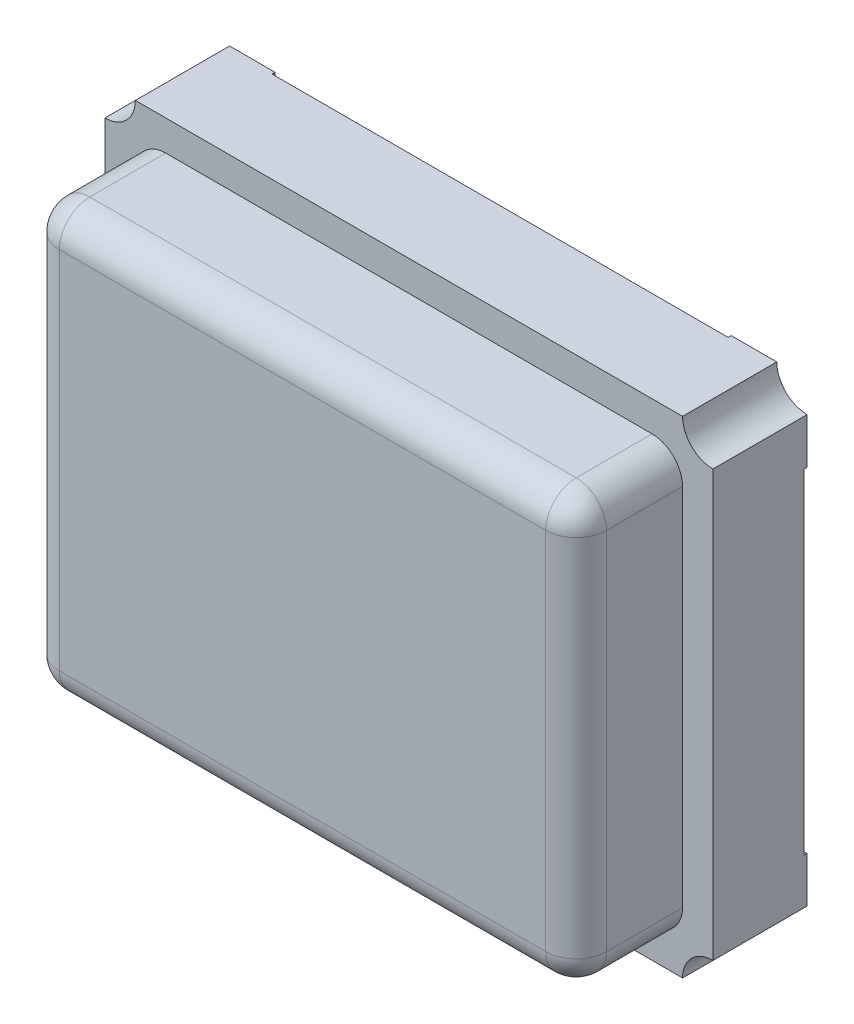
SolidWorks part; units mm, degrees
ref_plane "Front Plane" through (0, 0, 0) normal (0, 0, 1) x (1, 0, 0)
ref_plane "Top Plane" through (0, 0, 0) normal (0, 1, 0) x (1, 0, 0)
ref_plane "Right Plane" through (0, 0, 0) normal (1, 0, 0) x (0, 0, -1)
sketch "Sketch1" plane through (0, 0, 0) normal (0, 0, 1) x (1, 0, 0)
  line L1 (0, 0) -> (2, 0)
  line L2 (0, 0) -> (0, 1.6)
  line L3 (0, 1.6) -> (2, 1.6)
  line L4 (2, 0) -> (2, 1.6)
  dimension "D1" = 2
  dimension "D2" = 1.6
extrude "Boss-Extrude1" add sketch "Sketch1" along normal blind 0.3
sketch "Sketch2" plane through (0, 0, 0.3) normal (0, 0, 1) x (1, 0, 0)
  line L0 (1, 1.6) -> (1, 0) construction
  line L1 (0.1, 0.1) -> (1.9, 0.1)
  line L2 (0.1, 0.1) -> (0.1, 1.5)
  line L3 (0.1, 1.5) -> (1.9, 1.5)
  line L4 (1.9, 0.1) -> (1.9, 1.5)
  line L5 (2, 1.6) -> (0, 1.6) construction
  line L6 (0, 0) -> (2, 0) construction
  line L8 (0, 1.6) -> (0, 0) construction
  line L9 (0, 0.8) -> (2, 0.8) construction
  line L10 (2, 0) -> (2, 1.6) construction
  point P10 (1, 1.5)
  point P17 (0.1, 0.8)
  dimension "D1" = 1.8
  dimension "D2" = 1.4
extrude "Boss-Extrude2" add sketch "Sketch2" along normal blind 0.35
fillet "Fillet1" radius 0.1 4 edges at (1.9, 1.5, 0.475) (0.1, 1.5, 0.475) (0.1, 0.1, 0.475) (1.9, 0.1, 0.475)
sketch "Sketch3" plane through (0, 0, 0.3) normal (0, 0, 1) x (1, 0, 0)
  line L0 (0, 1.6) -> (0.1, 1.6)
  line L1 (0, 1.6) -> (2, 1.6) construction
  line L2 (0, 1.6) -> (0, 1.5)
  line L3 (0, 0) -> (0, 1.6) construction
  line L4 (0, 0) -> (0, 0.1)
  line L5 (0, 0) -> (0.1, 0)
  line L6 (0, 0) -> (2, 0) construction
  line L7 (2, 1.6) -> (1.9, 1.6)
  line L8 (2, 1.6) -> (2, 1.5)
  line L9 (2, 0) -> (2, 1.6) construction
  line L10 (2, 0) -> (2, 0.1)
  line L11 (2, 0) -> (1.9, 0)
  arc A0 (0, 1.5) -> (0.1, 1.6) centre (0, 1.6) ccw
  arc A1 (0, 0.1) -> (0.1, 0) centre (0, 0) cw
  arc A2 (1.9, 1.6) -> (2, 1.5) centre (2, 1.6) ccw
  arc A3 (1.9, 0) -> (2, 0.1) centre (2, 0) cw
extrude "Cut-Extrude1" cut sketch "Sketch3" against normal through all
sketch "Sketch4" plane through (0, 0, 0) normal (0, 0, -1) x (-1, 0, 0)
  line L0 (-2, 0.25) -> (-2, 0.1)
  line L1 (-2, 0.25) -> (-1.8991, 0.25)
  line L2 (0, 0) -> (-2, 0) construction
  line L3 (-1.75, 0) -> (-1.75, 0.1002)
  line L4 (-2, 0) -> (-2, 1.6) construction
  line L5 (-1.9, 0) -> (-1.75, 0)
  line L6 (-0.25, 0) -> (-0.1, 0)
  line L7 (0, 0) -> (0, 1.6) construction
  line L8 (0, 0.25) -> (-0.1, 0.25)
  line L9 (-0.25, 0) -> (-0.25, 0.1)
  line L10 (0, 0.25) -> (0, 0.1)
  line L11 (-1.8991, 0.1002) -> (-1.3991, 0.1002)
  line L12 (-1.8991, 1.0002) -> (-1.3991, 1.0002)
  line L13 (-1.8991, 1.0002) -> (-1.8991, 1.5002)
  line L14 (-1.8991, 1.5002) -> (-1.3991, 1.5002)
  line L15 (-1.3991, 1.0002) -> (-1.3991, 1.5002)
  line L16 (-1.8991, 1.0002) -> (-1.3991, 1.5002) construction
  line L17 (-1.8991, 1.5002) -> (-1.3991, 1.0002) construction
  line L18 (-1.8991, 0.1002) -> (-1.8991, 0.6002)
  line L19 (-1.8991, 0.6002) -> (-1.3991, 0.6002)
  line L20 (-1.3991, 0.1002) -> (-1.3991, 0.6002)
  line L21 (-1.8991, 0.1002) -> (-1.3991, 0.6002) construction
  line L22 (-1.8991, 0.6002) -> (-1.3991, 0.1002) construction
  line L23 (-0.6, 1) -> (-0.1, 1)
  line L24 (-0.6, 1) -> (-0.6, 1.5)
  line L25 (-0.6, 1.5) -> (-0.1, 1.5)
  line L26 (-0.1, 1) -> (-0.1, 1.5)
  line L27 (-0.6, 1) -> (-0.1, 1.5) construction
  line L28 (-0.6, 1.5) -> (-0.1, 1) construction
  line L29 (-0.6, 0.1) -> (-0.1, 0.1)
  line L30 (-0.6, 0.1) -> (-0.6, 0.6)
  line L31 (-0.6, 0.6) -> (-0.1, 0.6)
  line L32 (-0.1, 0.1) -> (-0.1, 0.6)
  line L33 (-0.6, 0.1) -> (-0.1, 0.6) construction
  line L34 (-0.6, 0.6) -> (-0.1, 0.1) construction
  line L35 (-0.25, 1.6) -> (-0.1, 1.6)
  line L36 (0, 1.6) -> (-2, 1.6) construction
  line L37 (-1.4521, 0.6532) -> (-0.653, 1.053)
  line L38 (-0.25, 1.6) -> (-0.25, 1.5)
  line L39 (0, 1.35) -> (0, 1.5)
  line L40 (-1.3461, 0.5472) -> (-1.3991, 0.5206)
  line L41 (-1.3461, 0.5472) -> (-0.547, 0.947)
  line L42 (-0.547, 0.947) -> (-0.441, 1)
  line L43 (-0.653, 1.053) -> (-0.6, 1.0796)
  line L44 (-1.4521, 0.6532) -> (-1.5582, 0.6002)
  line L45 (0, 1.35) -> (-0.1, 1.35)
  line L46 (-2, 1.35) -> (-2, 1.5)
  line L47 (-1.75, 1.6) -> (-1.9, 1.6)
  line L48 (-2, 1.35) -> (-1.8991, 1.35)
  line L49 (-1.75, 1.6) -> (-1.75, 1.5002)
  arc A0 (-2, 0.1) -> (-1.9, 0) centre (-2, 0) cw
  arc A1 (-0.1, 0) -> (0, 0.1) centre (0, 0) cw
  arc A2 (-0.1, 1.6) -> (0, 1.5) centre (0, 1.6) ccw
  arc A3 (-2, 1.5) -> (-1.9, 1.6) centre (-2, 1.6) ccw
  arc M16 (-0.1, 0) -> (0, 0.1) centre (0, 0) cw
  line M17 (0, 0.1) -> (0, 1.5)
  arc M18 (0, 1.5) -> (-0.1, 1.6) centre (0, 1.6) cw
  line M19 (-0.1, 1.6) -> (-1.9, 1.6)
  arc M20 (-1.9, 1.6) -> (-2, 1.5) centre (-2, 1.6) cw
  line M21 (-2, 1.5) -> (-2, 0.1)
  arc M22 (-2, 0.1) -> (-1.9, 0) centre (-2, 0) cw
  line M23 (-1.9, 0) -> (-0.1, 0)
extrude "Boss-Extrude3" add sketch "Sketch4" along normal blind 0.01 contours L49 L48 L13 L14 M19 M20 M21 | L12 L15 L14 L13 | L11 L20 L19 L18 | L11 L18 L1 L3 M21 M22 M23 | L37 L44 L19 L20 L40 L41 L42 L23 L24 L43 | L29 L32 L31 L30 | L23 L26 L25 L24 | L45 L38 L25 L26 M17 M18 M19 | L32 L29 L9 L8 M23 M16 M17
fillet "Fillet2" radius 0.1 8 edges at (0.1, 0.8, 0.65) (0.1293, 0.1293, 0.65) (1, 0.1, 0.65) (1.8707, 0.1293, 0.65) (1.9, 0.8, 0.65) (0.1293, 1.4707, 0.65) (1.8707, 1.4707, 0.65) (1, 1.5, 0.65)
